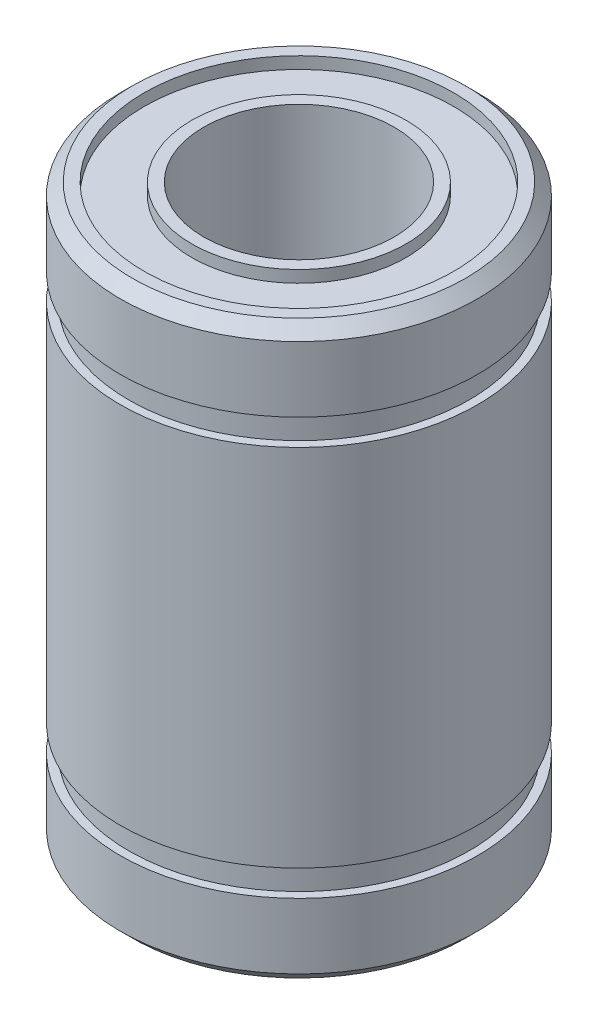
SolidWorks part; units mm, degrees
ref_plane "Front Plane" through (0, 0, 0) normal (0, 0, 1) x (1, 0, 0)
ref_plane "Top Plane" through (0, 0, 0) normal (0, 1, 0) x (1, 0, 0)
ref_plane "Right Plane" through (0, 0, 0) normal (1, 0, 0) x (0, 0, -1)
sketch "Sketch1" plane through (0, 0, 0) normal (0, 0, 1) x (1, 0, 0)
  line L0 (0, 12) -> (0, 0) construction
  line L1 (0, 0) -> (0, -12) construction
  line L2 (0, 12) -> (4, 12) construction
  line L3 (0, -12) -> (4, -12) construction
  line L4 (4, -12) -> (4, 12)
  line L5 (4, 12) -> (7, 12)
  line L6 (7, 12) -> (7.5, 11.5)
  line L7 (7.5, 11.5) -> (7.5, 8.75)
  line L8 (7.5, 7.65) -> (7.5, 8.75) construction
  line L9 (7.5, -8.75) -> (7.5, -7.65) construction
  line L10 (7.5, 7.65) -> (7.5, -7.65)
  line L11 (7.5, -11.5) -> (7, -11.5) construction
  line L12 (7, -11.5) -> (7, -12) construction
  line L13 (7.5, -8.75) -> (7.5, -11.5)
  line L14 (7.5, -11.5) -> (7, -12)
  line L15 (7, -12) -> (4, -12)
  line L16 (7.5, 11.5) -> (7, 11.5) construction
  line L17 (7, 11.5) -> (7, 12) construction
  line L18 (7, -11.5) -> (7, 11.5) construction
  line L19 (7.7571, -8.2) -> (7.7571, 8.2) construction
  line L20 (7.15, -8.2) -> (7.7571, -8.2) construction
  line L21 (7.5, 8.75) -> (7.15, 8.75)
  line L22 (0, 0) -> (7.5, 0) construction
  line L23 (7.15, 8.75) -> (7.15, 7.65)
  line L24 (7.15, 7.65) -> (7.5, 7.65)
  line L25 (7.5, -7.65) -> (7.15, -7.65)
  line L26 (7.15, -7.65) -> (7.15, -8.75)
  line L27 (7.15, -8.75) -> (7.5, -8.75)
  arc A0 (7.5, 8.75) -> (7.5, 7.65) centre (7.7571, 8.2) ccw construction
  arc A1 (7.5, -7.65) -> (7.5, -8.75) centre (7.7571, -8.2) ccw construction
  dimension "Total_length" = 24
  dimension "Inside_diameter" = 8
  dimension "D4" = 0.5
  dimension "Distance_between_lockingrings" = 17.5
  dimension "Diameter_outside" = 15
  dimension "Locking_ring_width" = 1.1
  dimension "Locking_ring_groove_dia" = 14.3
revolve "Body" add sketch "Sketch1" angle 360 about L0
sketch "Sketch2" plane through (0, 12, 0) normal (0, 1, 0) x (1, 0, 0)
  circle A0 centre (0, 0) radius 4.5
  circle A1 centre (0, 0) radius 6.5
  circle A2 centre (0, 0) radius 7.5 construction
  circle A3 centre (0, 0) radius 4 construction
  dimension "D1" = 1
  dimension "D2" = 0.5
extrude "Cut-Extrude1" cut sketch "Sketch2" against normal blind 0.5
mirror "Mirror1" about plane through (0, 0, 0) normal (0, 1, 0) of "Cut-Extrude1"
sketch "Sketch3" plane through (0, -11.5, 0) normal (0, -1, 0) x (1, 0, 0)
  line L0 (6.5, 0) -> (4.5, 0) construction
  circle A0 centre (0, 0) radius 5.1 construction
  circle A2 centre (0, 0) radius 6.5 construction
  circle A3 centre (0, 0) radius 4.5 construction
  text T0 "LM8UU Lineare bearing" font "Century Gothic" height 0.8
  point P11 (5.5, 0)
  dimension "D1" = 0.4
split line "Split Line1"
